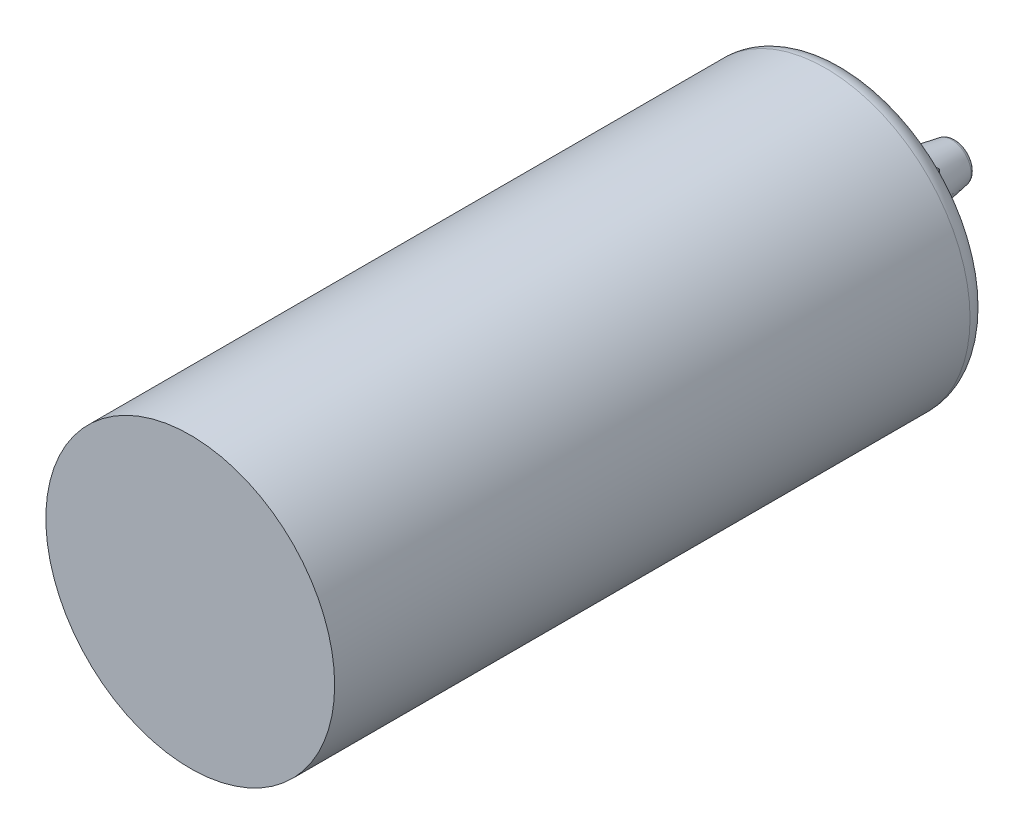
SolidWorks part; units mm, degrees
ref_plane "Front Plane" through (0, 0, 0) normal (0, 0, 1) x (1, 0, 0)
ref_plane "Top Plane" through (0, 0, 0) normal (0, 1, 0) x (1, 0, 0)
ref_plane "Right Plane" through (0, 0, 0) normal (1, 0, 0) x (0, 0, -1)
sketch "Sketch1" plane through (0, 0, 0) normal (0, 0, 1) x (1, 0, 0)
  circle A0 centre (0, 0) radius 19.05
  dimension "D1" = 38.1
extrude "Boss-Extrude1" add sketch "Sketch1" along normal blind 86.36
sketch "Sketch2" plane through (0, 0, 0) normal (0, 0, -1) x (-1, 0, 0)
  line L1 (-11.43, -11.43) -> (11.43, -11.43)
  line L2 (-11.43, -11.43) -> (-11.43, 11.43)
  line L3 (-11.43, 11.43) -> (11.43, 11.43)
  line L4 (11.43, -11.43) -> (11.43, 11.43)
  line L5 (-11.43, -11.43) -> (11.43, 11.43) construction
  line L6 (-11.43, 11.43) -> (11.43, -11.43) construction
  point P0 (0, 0)
  dimension "D1" = 22.86
extrude "Boss-Extrude2" add sketch "Sketch2" along normal blind 1.27 draft 10
fillet "Fillet1" radius 2.54 1 edges at (19.05, 0, 0)
sketch "Sketch3" plane through (0, 0, -1.27) normal (0, 0, -1) x (-1, 0, 0)
  line L1 (-5.715, 5.715) -> (5.715, 5.715) construction
  line L2 (-5.715, 5.715) -> (-5.715, -5.715) construction
  line L3 (-5.715, -5.715) -> (5.715, -5.715) construction
  line L4 (5.715, 5.715) -> (5.715, -5.715) construction
  line L5 (-5.715, 5.715) -> (5.715, -5.715) construction
  line L6 (-5.715, -5.715) -> (5.715, 5.715) construction
  circle A0 centre (-5.715, 5.715) radius 3.81
  circle A1 centre (5.715, 5.715) radius 3.81
  circle A2 centre (-5.715, -5.715) radius 3.81
  circle A3 centre (5.715, -5.715) radius 3.81
  point P8 (0, 0)
  dimension "D2" = 7.62
  dimension "D1" = 11.43
extrude "Boss-Extrude3" add sketch "Sketch3" along normal blind 7.62 draft 10
fillet "Fillet2" radius 0.635 4 edges at (3.2486, -5.715, -8.89) (-8.1814, -5.715, -8.89) (-8.1814, 5.715, -8.89) (3.2486, 5.715, -8.89)
sketch "Sketch4" plane through (0, 0, -8.89) normal (0, 0, -1) x (-1, 0, 0)
  circle A0 centre (-5.715, 5.715) radius 1.27
  circle A1 centre (5.715, 5.715) radius 1.27
  circle A2 centre (5.715, -5.715) radius 1.27
  circle A3 centre (-5.715, -5.715) radius 1.27
  circle A4 centre (-5.715, -5.715) radius 1.9336 construction
  dimension "D1" = 2.54
extrude "Cut-Extrude1" cut sketch "Sketch4" against normal blind 15.24 draft 5
